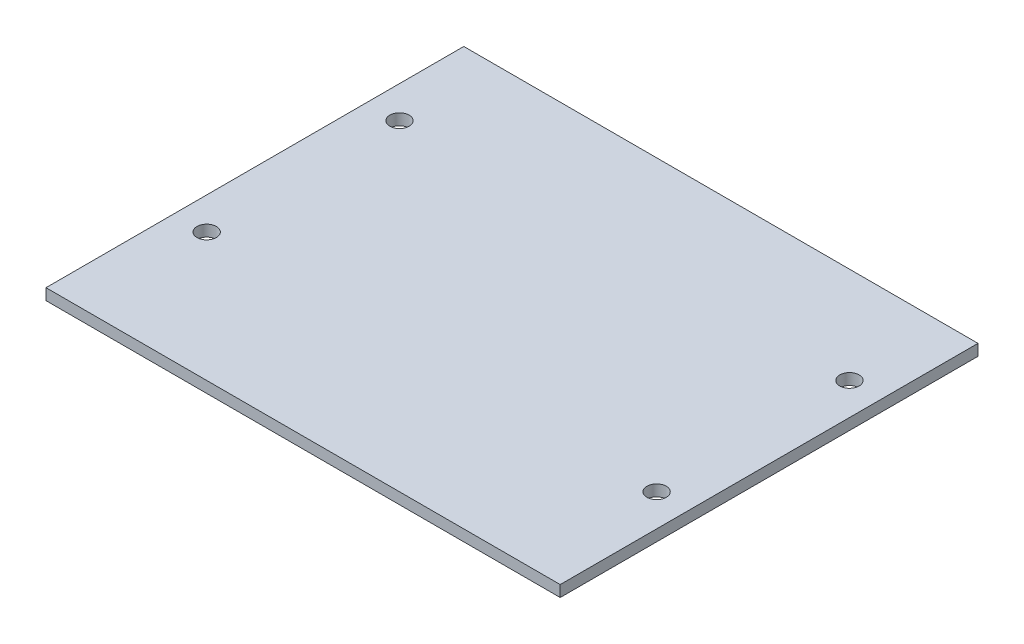
SolidWorks part; units mm, degrees
material "Custom FR4"
ref_plane "Front Plane" through (0, 0, 0) normal (0, 0, 1) x (1, 0, 0)
ref_plane "Top Plane" through (0, 0, 0) normal (0, 1, 0) x (1, 0, 0)
ref_plane "Right Plane" through (0, 0, 0) normal (1, 0, 0) x (0, 0, -1)
sketch "Sketch1" plane through (0, 0, 0) normal (0, 1, 0) x (1, 0, 0)
  line L0 (-40, 32.5) -> (40, -32.5) construction
  line L1 (-40, 32.5) -> (40, 32.5)
  line L2 (-40, 32.5) -> (-40, -32.5)
  line L3 (-40, -32.5) -> (40, -32.5)
  line L4 (40, 32.5) -> (40, -32.5)
  line L5 (-35, -12.5) -> (35, -12.5) construction
  line L6 (-35, 17.5) -> (35, 17.5) construction
  line L7 (-35, 17.5) -> (-35, -12.5) construction
  line L8 (35, 17.5) -> (35, -12.5) construction
  line L9 (-40, 14.15) -> (40, 14.15) construction
  circle A0 centre (-35, -12.5) radius 1.5025
  circle A1 centre (35, -12.5) radius 1.5025
  circle A2 centre (35, 17.5) radius 1.5025
  circle A3 centre (-35, 17.5) radius 1.5025
  point P15 (0, 14.15)
  dimension "D5" = 3.005
  dimension "D1" = 80
  dimension "D2" = 65
  dimension "D3" = 30
  dimension "D4" = 70
  dimension "D6" = 5
  dimension "D7" = 15
  dimension "D8" = 18.35
extrude "Boss-Extrude1" add sketch "Sketch1" along normal blind 1.75
